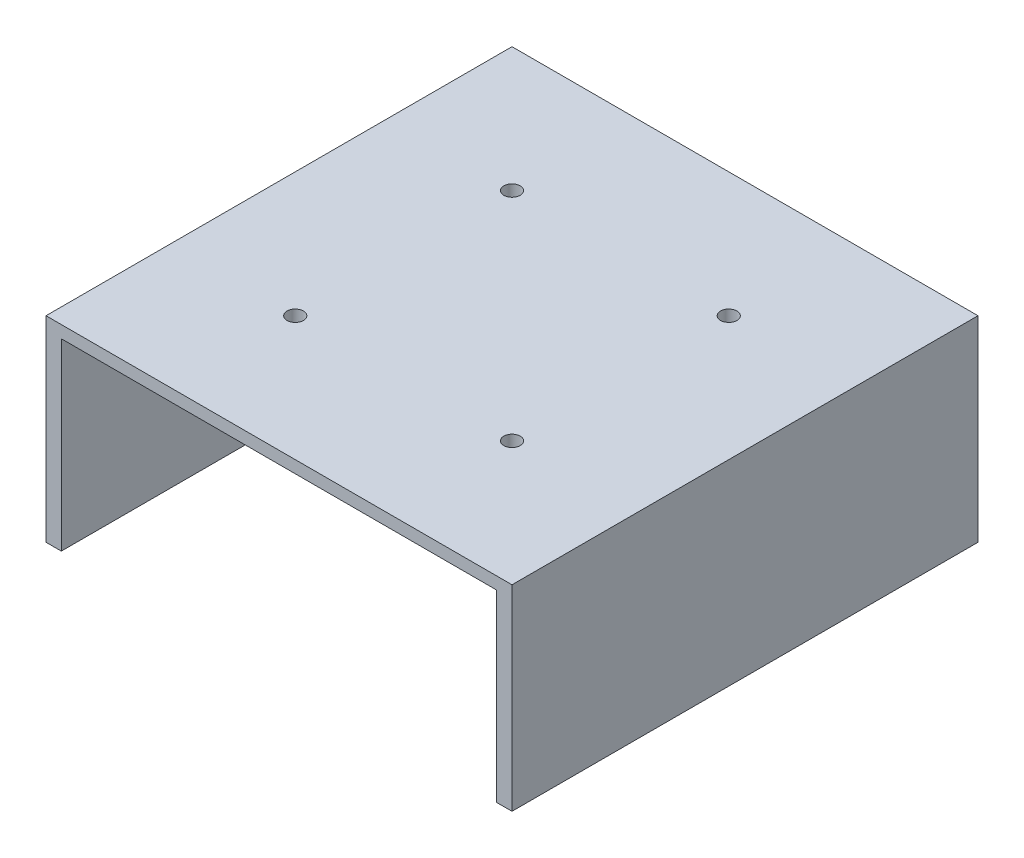
SolidWorks part; units mm, degrees
ref_plane "Front Plane" through (0, 0, 0) normal (0, 0, 1) x (1, 0, 0)
ref_plane "Top Plane" through (0, 0, 0) normal (0, 1, 0) x (1, 0, 0)
ref_plane "Right Plane" through (0, 0, 0) normal (1, 0, 0) x (0, 0, -1)
sketch "Sketch1" plane through (0, 0, 0) normal (0, 1, 0) x (1, 0, 0)
  line L0 (-22.4479, 22.4479) -> (22.4479, 22.4479) construction
  line L1 (-48.26, 48.26) -> (48.26, 48.26)
  line L2 (-48.26, 48.26) -> (-48.26, -48.26)
  line L3 (-48.26, -48.26) -> (48.26, -48.26)
  line L4 (48.26, 48.26) -> (48.26, -48.26)
  line L5 (-48.26, 48.26) -> (48.26, -48.26) construction
  line L6 (-48.26, -48.26) -> (48.26, 48.26) construction
  line L7 (-22.4479, 22.4479) -> (-22.4479, -22.4479) construction
  line L8 (-22.4479, -22.4479) -> (22.4479, -22.4479) construction
  line L9 (22.4479, 22.4479) -> (22.4479, -22.4479) construction
  line L10 (-22.4479, 22.4479) -> (22.4479, -22.4479) construction
  line L11 (-22.4479, -22.4479) -> (22.4479, 22.4479) construction
  circle A0 centre (-22.4479, 22.4479) radius 1.7
  circle A1 centre (22.4479, 22.4479) radius 1.7
  circle A2 centre (22.4479, -22.4479) radius 1.7
  circle A3 centre (-22.4479, -22.4479) radius 1.7
  point P0 (0, 0)
  point P6 (0, 0)
  point P11 (22.4479, -22.4479)
  point P12 (22.4479, 22.4479)
  point P13 (-22.4479, 22.4479)
  point P14 (-22.4479, -22.4479)
  dimension "D7" = 3.4
  dimension "D8" = 3.4
  dimension "D9" = 3.4
  dimension "D10" = 3.4
  dimension "D1" = 96.52
  dimension "D2" = 96.52
  dimension "D3" = 0
  dimension "D4" = 0
  dimension "D5" = 44.8958
  dimension "D6" = 44.8958
extrude "Boss-Extrude1" add sketch "Sketch1" along normal blind 2.54
sketch "Sketch2" plane through (0, 0, 0) normal (0, -1, 0) x (1, 0, 0)
  line L0 (48.26, -48.26) -> (-48.26, -48.26) construction
  line L1 (-48.26, 48.26) -> (-45.085, 48.26)
  line L2 (-48.26, 48.26) -> (-48.26, -48.26)
  line L3 (-48.26, -48.26) -> (-45.085, -48.26)
  line L4 (-45.085, 48.26) -> (-45.085, -48.26)
  line L6 (48.26, 48.26) -> (45.085, 48.26)
  line L7 (48.26, 48.26) -> (48.26, -48.26)
  line L8 (48.26, -48.26) -> (45.085, -48.26)
  line L9 (45.085, 48.26) -> (45.085, -48.26)
  dimension "D1" = 3.175
  dimension "D2" = 3.175
extrude "Boss-Extrude2" add sketch "Sketch2" along normal blind 38.1
